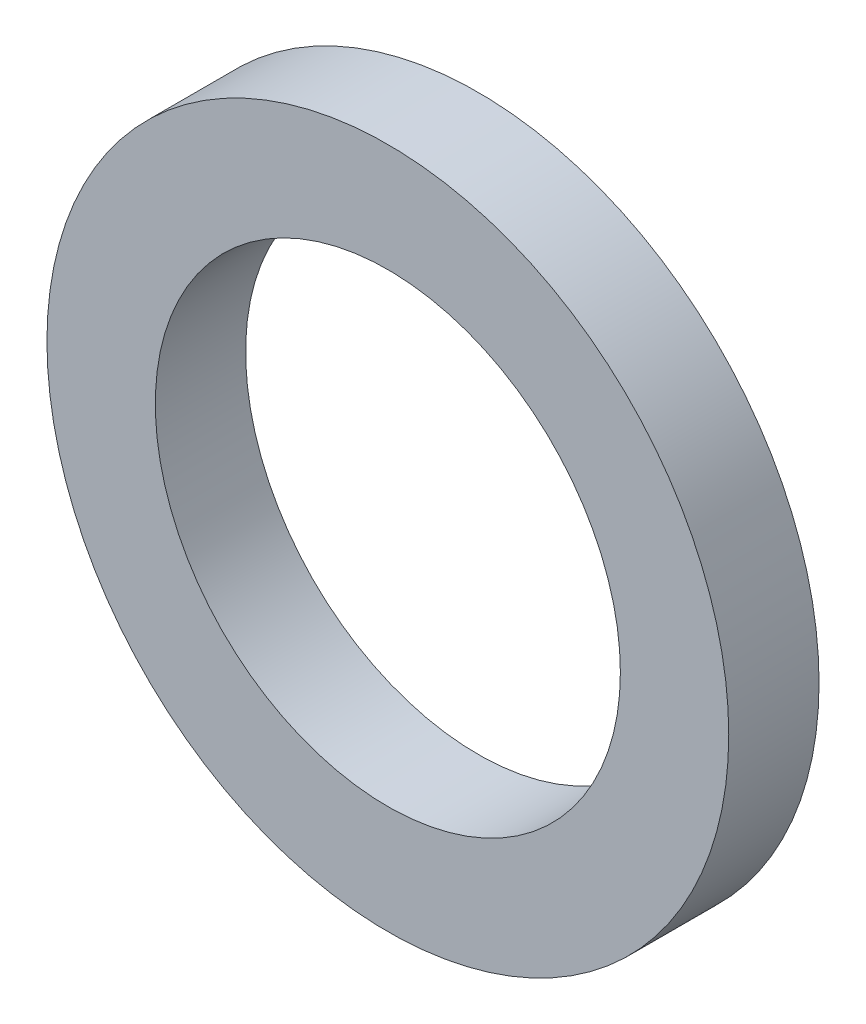
SolidWorks part; units mm, degrees
ref_plane "Front Plane" through (0, 0, 0) normal (0, 0, 1) x (1, 0, 0)
ref_plane "Top Plane" through (0, 0, 0) normal (0, 1, 0) x (1, 0, 0)
ref_plane "Right Plane" through (0, 0, 0) normal (1, 0, 0) x (0, 0, -1)
sketch "Sketch1" plane through (0, 0, 0) normal (0, 0, 1) x (1, 0, 0)
  circle A0 centre (0, 0) radius 2.575
  circle A1 centre (0, 0) radius 3.775
  dimension "D1" = 5.15
  dimension "D2" = 1.2
extrude "Boss-Extrude1" add sketch "Sketch1" along normal blind 1
